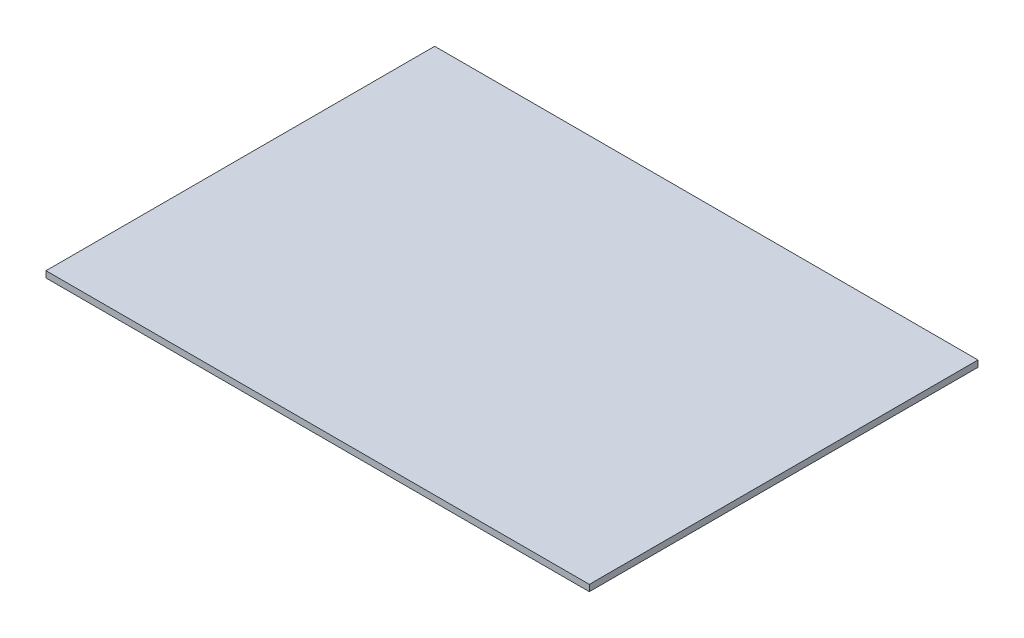
SolidWorks part; units mm, degrees
ref_plane "Front Plane" through (0, 0, 0) normal (0, 0, 1) x (1, 0, 0)
ref_plane "Top Plane" through (0, 0, 0) normal (0, 1, 0) x (1, 0, 0)
ref_plane "Right Plane" through (0, 0, 0) normal (1, 0, 0) x (0, 0, -1)
sketch "Sketch1" plane through (0, 0, 0) normal (0, 1, 0) x (1, 0, 0)
  line L1 (0, 0) -> (260, 0)
  line L2 (0, 0) -> (0, 186)
  line L3 (0, 186) -> (260, 186)
  line L4 (260, 0) -> (260, 186)
  dimension "D1" = 186
  dimension "D2" = 260
extrude "Boss-Extrude1" add sketch "Sketch1" along normal blind 3.048
